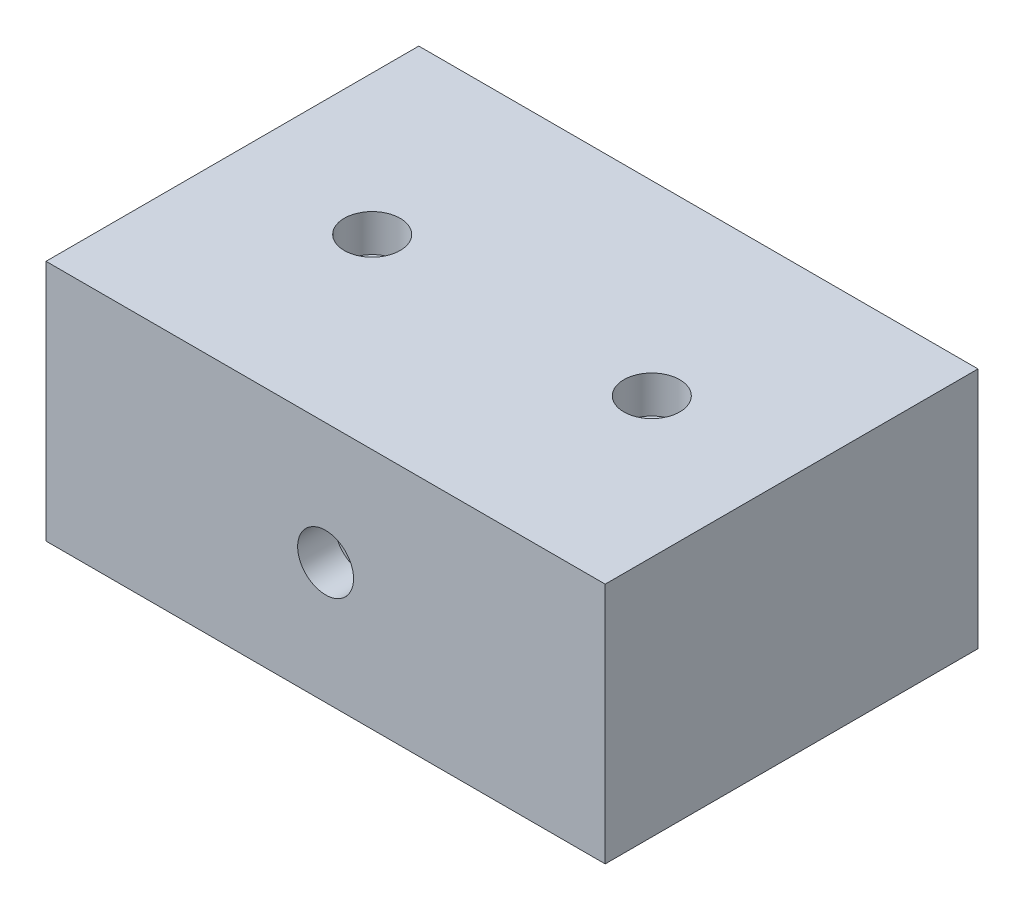
SolidWorks part; units mm, degrees
ref_plane "Front Plane" through (0, 0, 0) normal (0, 0, 1) x (1, 0, 0)
ref_plane "Top Plane" through (0, 0, 0) normal (0, 1, 0) x (1, 0, 0)
ref_plane "Right Plane" through (0, 0, 0) normal (1, 0, 0) x (0, 0, -1)
sketch "Sketch1" plane through (0, 0, 0) normal (0, 0, 1) x (1, 0, 0)
  line L1 (0, 0) -> (30, 0)
  line L2 (0, 0) -> (0, 13)
  line L3 (0, 13) -> (30, 13)
  line L4 (30, 0) -> (30, 13)
  dimension "D1" = 30
  dimension "D2" = 13
extrude "Boss-Extrude1" add sketch "Sketch1" along normal blind 20
sketch "Sketch2" plane through (0, 0, 20) normal (0, 0, 1) x (1, 0, 0)
  line L0 (15, 13) -> (15, 0) construction
  line L1 (30, 13) -> (0, 13) construction
  line L2 (0, 0) -> (30, 0) construction
  circle A0 centre (15, 6.5) radius 1.5
  dimension "D1" = 3
extrude "Cut-Extrude1" cut sketch "Sketch2" against normal blind 2
sketch "Sketch3" plane through (0, 13, 0) normal (0, 1, 0) x (1, 0, 0)
  line L1 (0, -20) -> (0, 0) construction
  line L2 (30, -20) -> (30, 0) construction
  line L3 (30, -10) -> (15, -10) construction
  line L4 (15, -10) -> (0, -10) construction
  line L5 (0, -10) -> (15, -10) construction
  line L6 (15, -10) -> (30, -10) construction
  circle A0 centre (7.5, -10) radius 1.5
  circle A1 centre (22.5, -10) radius 1.5
  dimension "D1" = 3
extrude "Cut-Extrude2" cut sketch "Sketch3" against normal blind 2
